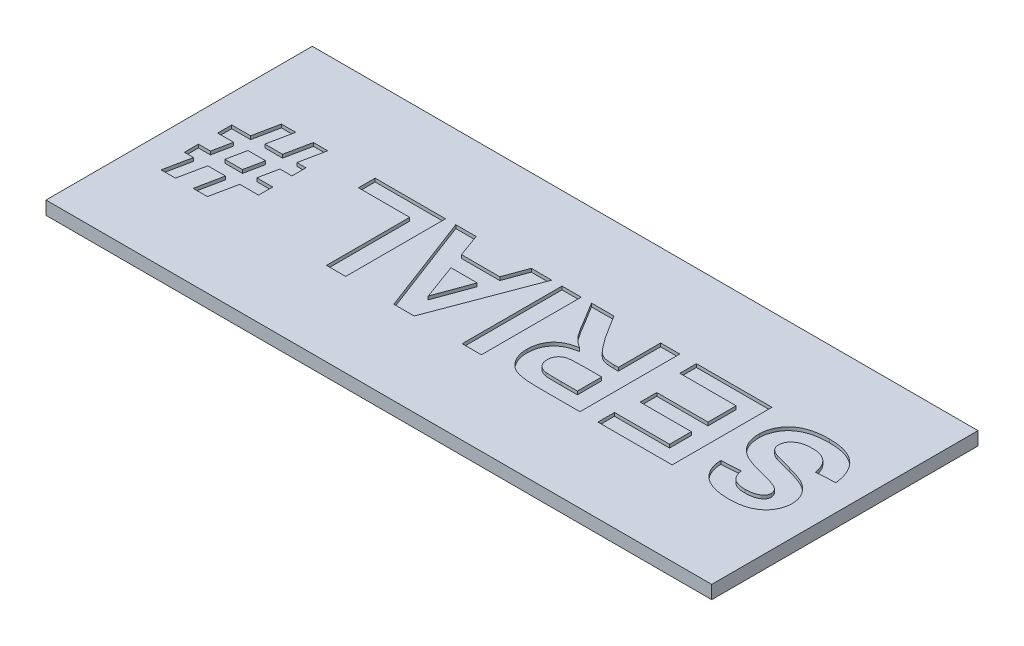
SolidWorks part; units mm, degrees
ref_plane "Front Plane" through (0, 0, 0) normal (0, 0, 1) x (1, 0, 0)
ref_plane "Top Plane" through (0, 0, 0) normal (0, 1, 0) x (1, 0, 0)
ref_plane "Right Plane" through (0, 0, 0) normal (1, 0, 0) x (0, 0, -1)
sketch "Sketch1" plane through (0, 0, 0) normal (0, 1, 0) x (1, 0, 0)
  line L1 (-100, -40) -> (100, -40)
  line L2 (-100, -40) -> (-100, 40)
  line L3 (-100, 40) -> (100, 40)
  line L4 (100, -40) -> (100, 40)
  line L5 (-100, -40) -> (100, 40) construction
  line L6 (-100, 40) -> (100, -40) construction
  point P0 (0, 0)
  dimension "D1" = 200
  dimension "D2" = 80
extrude "Boss-Extrude1" add sketch "Sketch1" along normal blind 4
sketch "Sketch2" plane through (0, 4, 0) normal (0, 1, 0) x (-1, 0, 0)
  text T0 "<b>SERIAL #</b>" font "Arial" height 30
extrude "Cut-Extrude1" cut sketch "Sketch2" against normal blind 1
